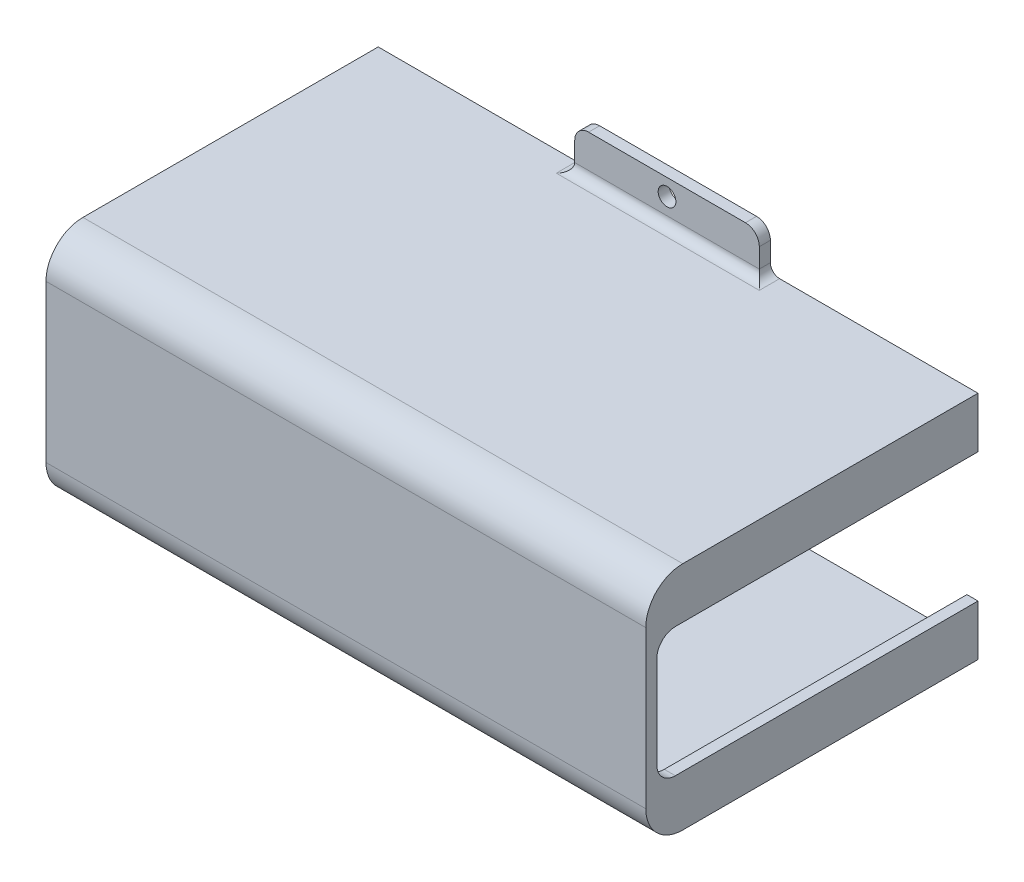
SolidWorks part; units mm, degrees
ref_plane "Front Plane" through (0, 0, 0) normal (0, 0, 1) x (1, 0, 0)
ref_plane "Top Plane" through (0, 0, 0) normal (0, 1, 0) x (1, 0, 0)
ref_plane "Right Plane" through (0, 0, 0) normal (1, 0, 0) x (0, 0, -1)
sketch "Sketch1" plane through (0, 0, 0) normal (0, 0, 1) x (1, 0, 0)
  line L1 (41.275, -15.875) -> (-41.275, -15.875)
  line L2 (41.275, -15.875) -> (41.275, 15.875)
  line L3 (41.275, 15.875) -> (-41.275, 15.875)
  line L4 (-41.275, -15.875) -> (-41.275, 15.875)
  line L5 (41.275, -15.875) -> (-41.275, 15.875) construction
  line L6 (41.275, 15.875) -> (-41.275, -15.875) construction
  point P0 (0, 0)
  dimension "D1" = 82.55
  dimension "D2" = 31.75
extrude "Boss-Extrude1" add sketch "Sketch1" along normal blind 45.72
shell "Shell1" thickness 1.524
sketch "Sketch3" plane through (0, 0, 0) normal (0, 0, -1) x (-1, 0, 0)
  line L0 (-41.275, 15.875) -> (41.275, 15.875) construction
  line L1 (-12.7, 15.875) -> (12.7, 15.875)
  line L2 (-12.7, 15.875) -> (-12.7, 21.717)
  line L3 (-12.7, 21.717) -> (12.7, 21.717)
  line L4 (12.7, 15.875) -> (12.7, 21.717)
  line L5 (41.275, -15.875) -> (-41.275, -15.875) construction
  line L6 (-12.7, -15.875) -> (12.7, -15.875)
  line L7 (-12.7, -15.875) -> (-12.7, -21.717)
  line L8 (-12.7, -21.717) -> (12.7, -21.717)
  line L9 (12.7, -15.875) -> (12.7, -21.717)
  point P13 (0, 21.717)
  point P14 (0, 15.875)
  dimension "D1" = 5.842
  dimension "D2" = 25.4
extrude "Boss-Extrude3" add sketch "Sketch3" against normal blind 1.524
fillet "Fillet2" radius 1.27 6 edges at (12.7, -15.875, 0.762) (-12.7, -15.875, 0.762) (0, -15.875, 1.524) (-12.7, 15.875, 0.762) (12.7, 15.875, 0.762) (0, 15.875, 1.524)
fillet "Fillet3" radius 1.905 4 edges at (-12.7, -21.717, 0.762) (12.7, -21.717, 0.762) (12.7, 21.717, 0.762) (-12.7, 21.717, 0.762)
hole_wizard "#2 Clearance Hole1" positions "Sketch4" profile "Sketch5" hole size "#2" standard "ANSI Inch" end condition through all
sketch "Sketch4" plane through (0, 0, 1.524) normal (0, 0, 1) x (1, 0, 0)
  line L0 (0, 21.717) -> (0, 17.145) construction
  line L1 (-10.795, 21.717) -> (10.795, 21.717) construction
  line L2 (-12.7, 17.145) -> (12.7, 17.145) construction
  line L4 (0, -21.717) -> (0, -17.145) construction
  line L5 (10.795, -21.717) -> (-10.795, -21.717) construction
  line L6 (12.7, -17.145) -> (-12.7, -17.145) construction
  point P0 (0, 19.431)
  point P2 (0, -19.431)
  point P14 (0, 19.431)
  point P23 (0, -19.431)
sketch "Sketch5" plane through (0, 19.431, 1.524) normal (1, 0, 0) x (0, -1, 0)
  line L0 (0, 0) -> (0, 1.524)
  line L1 (0, 1.524) -> (1.2192, 1.524)
  line L2 (1.2192, 1.524) -> (1.2192, 0)
  line L5 (1.2192, 0) -> (0, 0)
  line L11 (0, -6.35) -> (0, 107.95) construction
  dimension "Thru Hole Dia." = 2.4384
  dimension "Thru Hole Depth" = 1.524
sketch "Sketch6" plane through (-39.751, 0, 0) normal (1, 0, 0) x (0, 0, -1)
  line L4 (0, -14.351) -> (0, 14.351)
  line L5 (0, 14.351) -> (-44.196, 14.351)
  line L6 (-44.196, 14.351) -> (-44.196, -14.351)
  line L7 (-44.196, -14.351) -> (0, -14.351)
  line L8 (0, -14.351) -> (0, 14.351)
  line L9 (0, 14.351) -> (-44.196, 14.351)
  line L10 (-44.196, 14.351) -> (-44.196, -14.351)
  line L11 (-44.196, -14.351) -> (0, -14.351)
  dimension "D1" = 0
extrude "Cut-Extrude1" cut sketch "Sketch6" against normal through all both and the other way through all
fillet "Fillet4" radius 3.556 2 edges at (0, -14.351, 44.196) (0, 14.351, 44.196)
fillet "Fillet5" radius 5.08 2 edges at (0, -15.875, 45.72) (0, 15.875, 45.72)
sketch "Sketch7" plane through (41.275, 0, 0) normal (1, 0, 0) x (0, 0, -1)
  line L0 (-40.64, -15.875) -> (0, -15.875) construction
  line L1 (-45.72, 10.795) -> (-45.72, -10.795)
  line L2 (-40.64, 15.875) -> (0, 15.875) construction
  line L3 (-40.64, -15.875) -> (0, -15.875)
  line L5 (-40.64, 15.875) -> (0, 15.875)
  line L6 (0, 15.875) -> (0, 8.89)
  line L7 (0, 8.89) -> (-44.196, 8.89)
  line L8 (0, -15.875) -> (0, -8.89)
  line L9 (0, -8.89) -> (-44.196, -8.89)
  line L13 (-45.72, 0) -> (-38.735, 0) construction
  line L14 (-44.196, 10.795) -> (-44.196, -10.795) construction
  line L15 (-44.196, 8.89) -> (-44.196, -8.89)
  arc A0 (-45.72, -10.795) -> (-40.64, -15.875) centre (-40.64, -10.795) ccw construction
  arc A1 (-40.64, 15.875) -> (-45.72, 10.795) centre (-40.64, 10.795) ccw construction
  arc A2 (-45.72, -10.795) -> (-40.64, -15.875) centre (-40.64, -10.795) ccw
  arc A3 (-40.64, 15.875) -> (-45.72, 10.795) centre (-40.64, 10.795) ccw
  dimension "D1" = 6.985
extrude "Boss-Extrude4" add sketch "Sketch7" against normal blind 1.524
fillet "Fillet9" radius 2.54 2 edges at (40.513, -8.89, 44.196) (40.513, 8.89, 44.196)
mirror "Mirror1" about plane through (0, 0, 0) normal (1, 0, 0) of "Boss-Extrude4"
fillet "Fillet10" radius 2.54 2 edges at (-40.513, -8.89, 44.196) (-40.513, 8.89, 44.196)
